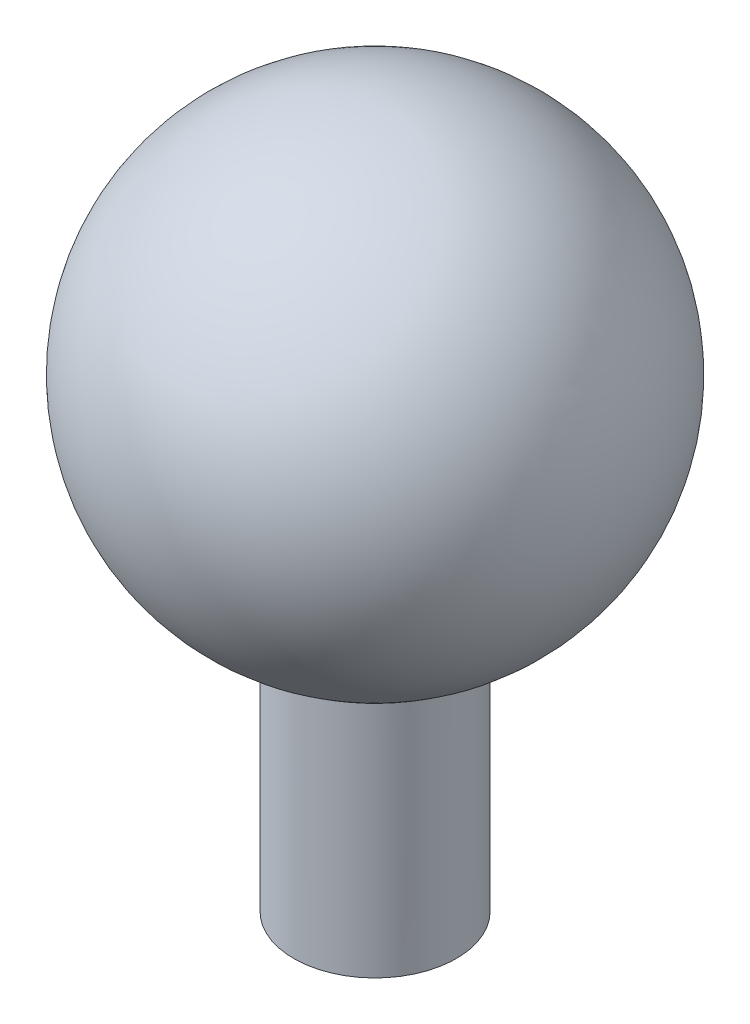
SolidWorks part; units mm, degrees
material "1060 Alloy"
ref_plane "Front Plane" through (0, 0, 0) normal (0, 0, 1) x (1, 0, 0)
ref_plane "Top Plane" through (0, 0, 0) normal (0, 1, 0) x (1, 0, 0)
ref_plane "Right Plane" through (0, 0, 0) normal (1, 0, 0) x (0, 0, -1)
sketch "Sketch1" plane through (0, 0, 0) normal (0, 0, 1) x (1, 0, 0)
  line L0 (0, 5) -> (0, -10)
  line L1 (0, -10) -> (-1.75, -10)
  line L2 (-1.75, -10) -> (-1.75, -4.6837)
  arc A0 (0, 5) -> (-1.75, -4.6837) centre (0, 0) ccw
  dimension "D1" = 10
  dimension "D2" = 1.75
  dimension "D3" = 15
revolve "Revolve1" add sketch "Sketch1" angle 360 about L0
ref_plane "Plane1" through (0, -9, 0) normal (0, -1, 0) x (-1, 0, 0)
sketch "Sketch2" plane through (0, -9, 0) normal (0, -1, 0) x (-1, 0, 0)
  line L0 (0, 1.75) -> (0, -1.75) construction
  circle A0 centre (0, 0) radius 1.75 construction
  circle A1 centre (0, 0) radius 1.75 construction
